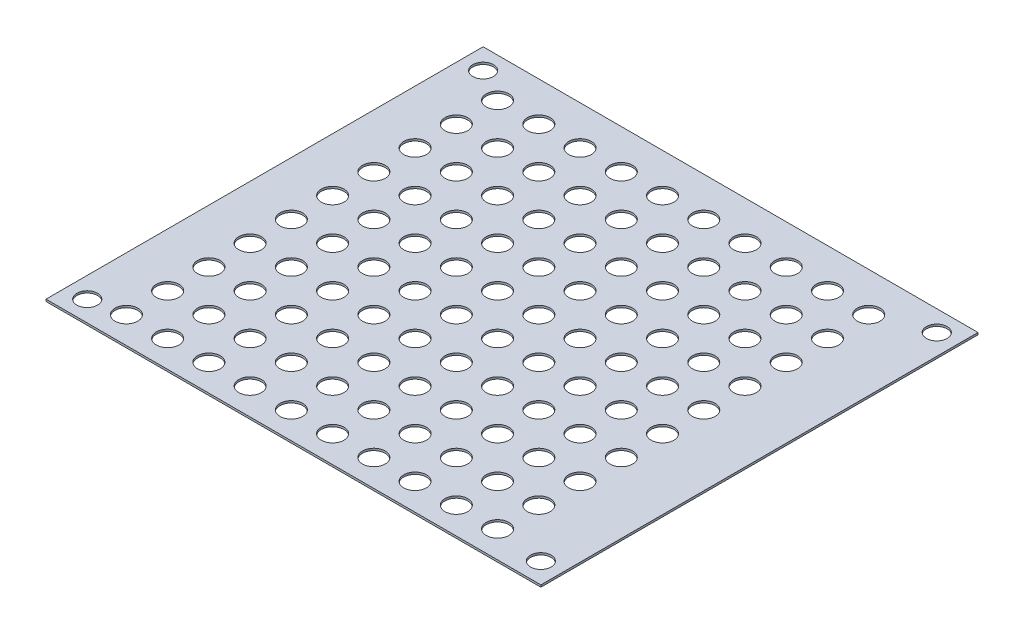
SolidWorks part; units mm, degrees
ref_plane "Front Plane" through (0, 0, 0) normal (0, 0, 1) x (1, 0, 0)
ref_plane "Top Plane" through (0, 0, 0) normal (0, 1, 0) x (1, 0, 0)
ref_plane "Right Plane" through (0, 0, 0) normal (1, 0, 0) x (0, 0, -1)
sketch "Sketch1" plane through (0, 0, 0) normal (0, 1, 0) x (1, 0, 0)
  line L0 (115, 101) -> (5, 101) construction
  line L1 (0, 0) -> (120, 0)
  line L2 (0, 0) -> (0, 106)
  line L3 (0, 106) -> (120, 106)
  line L4 (120, 0) -> (120, 106)
  line L6 (115, 101) -> (115, 5) construction
  circle A17 centre (13, 36.5) radius 2.75
  circle A18 centre (23, 36.5) radius 2.75
  circle A19 centre (13, 6.5) radius 2.75
  circle A28 centre (5, 5) radius 2.5
  circle A29 centre (5, 101) radius 2.5
  circle A30 centre (115, 101) radius 2.5
  circle A31 centre (115, 5) radius 2.5
  circle A32 centre (23, 6.5) radius 2.75
  circle A33 centre (33, 6.5) radius 2.75
  circle A34 centre (23, 16.5) radius 2.75
  circle A35 centre (33, 16.5) radius 2.75
  circle A36 centre (23, 26.5) radius 2.75
  circle A37 centre (33, 26.5) radius 2.75
  circle A38 centre (13, 16.5) radius 2.75
  circle A39 centre (13, 26.5) radius 2.75
  circle A40 centre (33, 36.5) radius 2.75
  circle A41 centre (13, 46.5) radius 2.75
  circle A42 centre (23, 46.5) radius 2.75
  circle A43 centre (33, 46.5) radius 2.75
  circle A44 centre (13, 56.5) radius 2.75
  circle A45 centre (23, 56.5) radius 2.75
  circle A46 centre (33, 56.5) radius 2.75
  circle A47 centre (13, 66.5) radius 2.75
  circle A48 centre (23, 66.5) radius 2.75
  circle A49 centre (33, 66.5) radius 2.75
  circle A50 centre (13, 76.5) radius 2.75
  circle A51 centre (23, 76.5) radius 2.75
  circle A52 centre (33, 76.5) radius 2.75
  circle A53 centre (13, 86.5) radius 2.75
  circle A54 centre (23, 86.5) radius 2.75
  circle A55 centre (33, 86.5) radius 2.75
  circle A56 centre (13, 96.5) radius 2.75
  circle A57 centre (23, 96.5) radius 2.75
  circle A58 centre (33, 96.5) radius 2.75
  circle A59 centre (43, 6.5) radius 2.75
  circle A60 centre (53, 6.5) radius 2.75
  circle A61 centre (63, 6.5) radius 2.75
  circle A62 centre (73, 6.5) radius 2.75
  circle A63 centre (83, 6.5) radius 2.75
  circle A64 centre (93, 6.5) radius 2.75
  circle A65 centre (103, 6.5) radius 2.75
  circle A66 centre (43, 16.5) radius 2.75
  circle A67 centre (53, 16.5) radius 2.75
  circle A68 centre (63, 16.5) radius 2.75
  circle A69 centre (73, 16.5) radius 2.75
  circle A70 centre (83, 16.5) radius 2.75
  circle A71 centre (93, 16.5) radius 2.75
  circle A72 centre (103, 16.5) radius 2.75
  circle A73 centre (43, 26.5) radius 2.75
  circle A74 centre (53, 26.5) radius 2.75
  circle A75 centre (63, 26.5) radius 2.75
  circle A76 centre (73, 26.5) radius 2.75
  circle A77 centre (83, 26.5) radius 2.75
  circle A78 centre (93, 26.5) radius 2.75
  circle A79 centre (103, 26.5) radius 2.75
  circle A80 centre (43, 36.5) radius 2.75
  circle A81 centre (53, 36.5) radius 2.75
  circle A82 centre (63, 36.5) radius 2.75
  circle A83 centre (73, 36.5) radius 2.75
  circle A84 centre (83, 36.5) radius 2.75
  circle A85 centre (93, 36.5) radius 2.75
  circle A86 centre (103, 36.5) radius 2.75
  circle A87 centre (43, 46.5) radius 2.75
  circle A88 centre (53, 46.5) radius 2.75
  circle A89 centre (63, 46.5) radius 2.75
  circle A90 centre (73, 46.5) radius 2.75
  circle A91 centre (83, 46.5) radius 2.75
  circle A92 centre (93, 46.5) radius 2.75
  circle A93 centre (103, 46.5) radius 2.75
  circle A94 centre (43, 56.5) radius 2.75
  circle A95 centre (53, 56.5) radius 2.75
  circle A96 centre (63, 56.5) radius 2.75
  circle A97 centre (73, 56.5) radius 2.75
  circle A98 centre (83, 56.5) radius 2.75
  circle A99 centre (93, 56.5) radius 2.75
  circle A100 centre (103, 56.5) radius 2.75
  circle A101 centre (43, 66.5) radius 2.75
  circle A102 centre (53, 66.5) radius 2.75
  circle A103 centre (63, 66.5) radius 2.75
  circle A104 centre (73, 66.5) radius 2.75
  circle A105 centre (83, 66.5) radius 2.75
  circle A106 centre (93, 66.5) radius 2.75
  circle A107 centre (103, 66.5) radius 2.75
  circle A108 centre (43, 76.5) radius 2.75
  circle A109 centre (53, 76.5) radius 2.75
  circle A110 centre (63, 76.5) radius 2.75
  circle A111 centre (73, 76.5) radius 2.75
  circle A112 centre (83, 76.5) radius 2.75
  circle A113 centre (93, 76.5) radius 2.75
  circle A114 centre (103, 76.5) radius 2.75
  circle A115 centre (43, 86.5) radius 2.75
  circle A116 centre (53, 86.5) radius 2.75
  circle A117 centre (63, 86.5) radius 2.75
  circle A118 centre (73, 86.5) radius 2.75
  circle A119 centre (83, 86.5) radius 2.75
  circle A120 centre (93, 86.5) radius 2.75
  circle A121 centre (103, 86.5) radius 2.75
  circle A122 centre (43, 96.5) radius 2.75
  circle A123 centre (53, 96.5) radius 2.75
  circle A124 centre (63, 96.5) radius 2.75
  circle A125 centre (73, 96.5) radius 2.75
  circle A126 centre (83, 96.5) radius 2.75
  circle A127 centre (93, 96.5) radius 2.75
  circle A128 centre (103, 96.5) radius 2.75
  point P7 (115, 53)
  point P9 (60, 101)
  point P10 (60, 106)
  point P20 (120, 53)
  dimension "D5" = 110
  dimension "D6" = 96
  dimension "D3" = 5.5
  dimension "D8" = 5
  dimension "D1" = 120
  dimension "D2" = 106
  dimension "D4" = 8
  dimension "D7" = 1.5
  dimension "D9" = 10
  dimension "D10" = 10
extrude "Boss-Extrude1" add sketch "Sketch1" along normal blind 0.5
equation "\"o\"= 10mm"
equation "\"P\"= 10"
